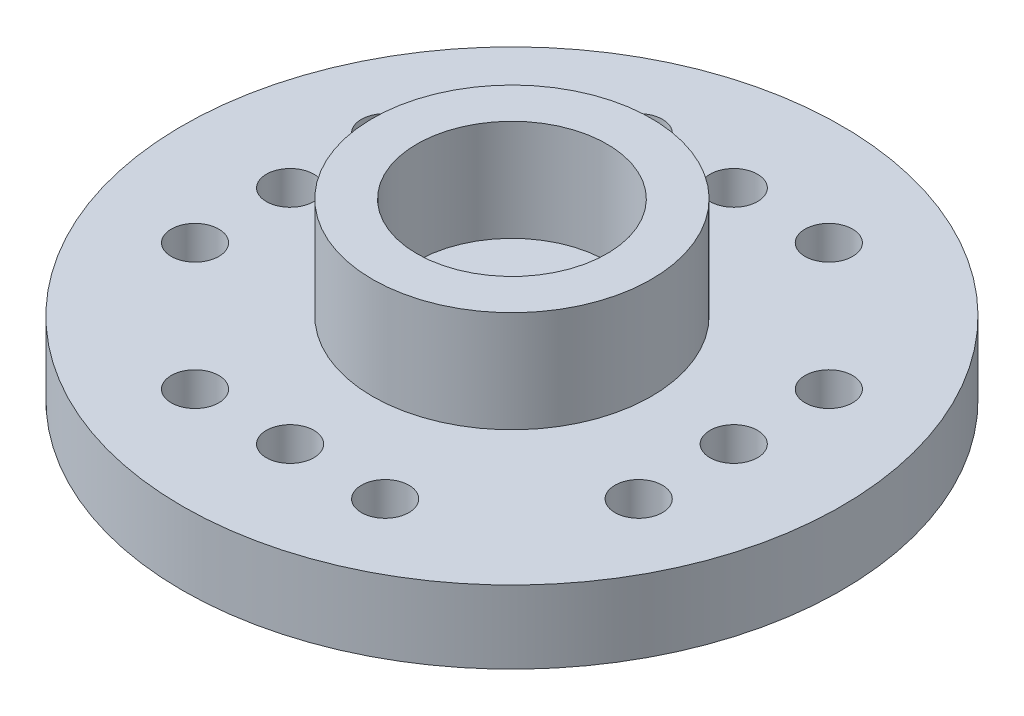
SolidWorks part; units mm, degrees
ref_plane "前视基准面" through (0, 0, 0) normal (0, 0, 1) x (1, 0, 0)
ref_plane "上视基准面" through (0, 0, 0) normal (0, 1, 0) x (1, 0, 0)
ref_plane "右视基准面" through (0, 0, 0) normal (1, 0, 0) x (0, 0, -1)
sketch "Sketch1" plane through (0, 0, 0) normal (0, 1, 0) x (1, 0, 0)
  line L1 (-7, 7) -> (7, 7) construction
  line L2 (-7, 7) -> (-7, -7) construction
  line L3 (-7, -7) -> (7, -7) construction
  line L4 (7, 7) -> (7, -7) construction
  line L5 (-7, 7) -> (7, -7) construction
  line L6 (-7, -7) -> (7, 7) construction
  circle A0 centre (0, 0) radius 10.4
  circle A1 centre (7, 0) radius 0.75
  circle A2 centre (7, 3) radius 0.75
  circle A3 centre (7, -3) radius 0.75
  circle A4 centre (3, -7) radius 0.75
  circle A5 centre (0, -7) radius 0.75
  circle A6 centre (-3, -7) radius 0.75
  circle A7 centre (-7, -3) radius 0.75
  circle A8 centre (-7, 0) radius 0.75
  circle A9 centre (-7, 3) radius 0.75
  circle A10 centre (-3, 7) radius 0.75
  circle A11 centre (0, 7) radius 0.75
  circle A12 centre (3, 7) radius 0.75
  circle A13 centre (0, 0) radius 1.5
  dimension "D3" = 20.8
  dimension "D4" = 1.5
  dimension "D5" = 3
  dimension "D6" = 3
  dimension "D7" = 3
  dimension "D1" = 14
  dimension "D2" = 14
extrude "Boss-Extrude1" add sketch "Sketch1" along normal blind 2.3
sketch "Sketch2" plane through (0, 2.3, 0) normal (0, 1, 0) x (1, 0, 0)
  circle A0 centre (0, 0) radius 4.4
  circle A1 centre (0, 0) radius 3
  dimension "D1" = 8.8
  dimension "D2" = 6
extrude "Boss-Extrude2" add sketch "Sketch2" along normal blind 3.2
